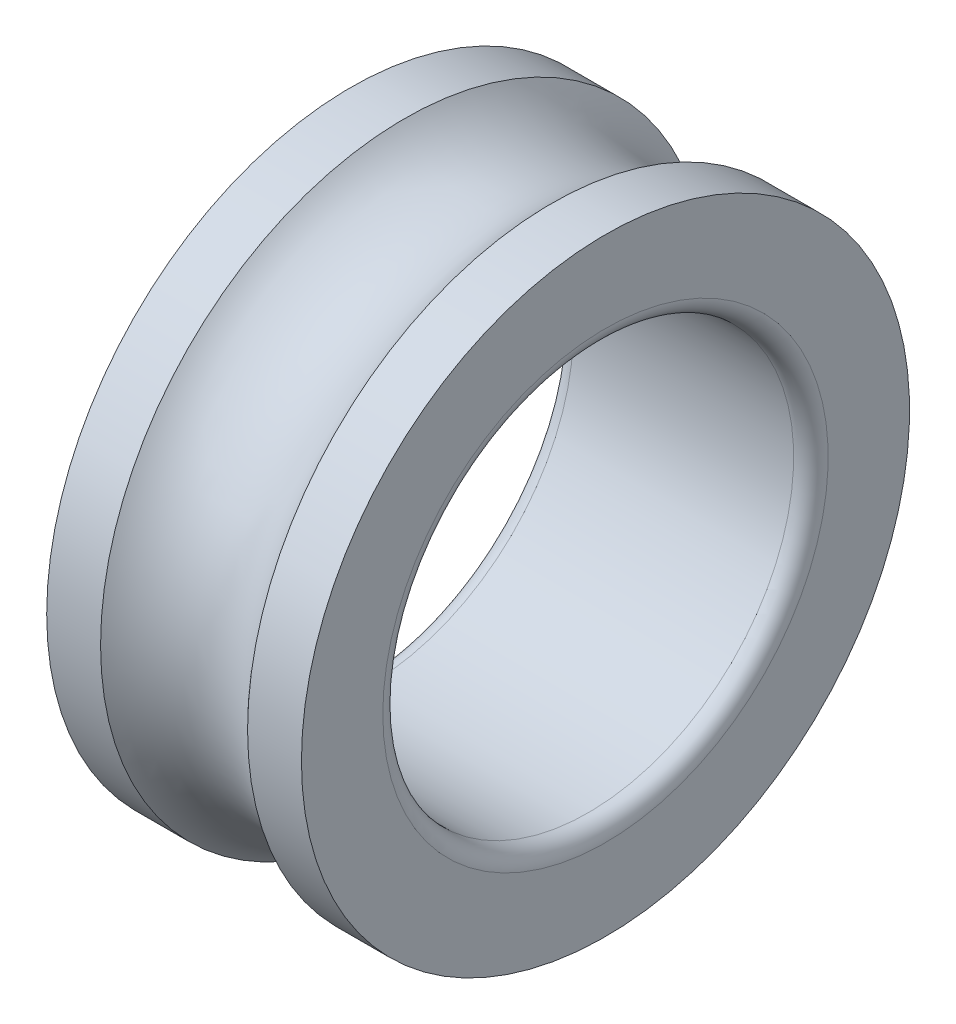
SolidWorks part; units mm, degrees
ref_plane "Front Plane" through (0, 0, 0) normal (0, 0, 1) x (1, 0, 0)
ref_plane "Top Plane" through (0, 0, 0) normal (0, 1, 0) x (1, 0, 0)
ref_plane "Right Plane" through (0, 0, 0) normal (1, 0, 0) x (0, 0, -1)
sketch "Sketch1" plane through (0, 0, 0) normal (0, 0, 1) x (1, 0, 0)
  line L0 (-11.8694, 0) -> (21.9234, 0) construction
  line L1 (0, 0) -> (0, 25) construction
  line L3 (-15.5, 37) -> (-15.5, 27.1)
  line L4 (-13.4, 25) -> (13.4, 25)
  line L5 (15.5, 37) -> (15.5, 27.1)
  line L6 (-15.5, 37) -> (15.5, 25) construction
  line L7 (-15.5, 25) -> (15.5, 37) construction
  line L8 (-8.9443, 37) -> (-15.5, 37)
  line L9 (8.9443, 37) -> (15.5, 37)
  arc A0 (8.9443, 37) -> (-8.9443, 37) centre (0, 45) cw
  arc A1 (13.4, 25) -> (15.5, 27.1) centre (13.4, 27.1) ccw
  arc A2 (-15.5, 27.1) -> (-13.4, 25) centre (-13.4, 27.1) ccw
  point P3 (0, 31)
  dimension "D5" = 12
  dimension "D3" = 2.1
  dimension "D1" = 31
  dimension "D2" = 25
  dimension "D4" = 9.9
revolve "Revolve1" add sketch "Sketch1" angle 360 about L0
